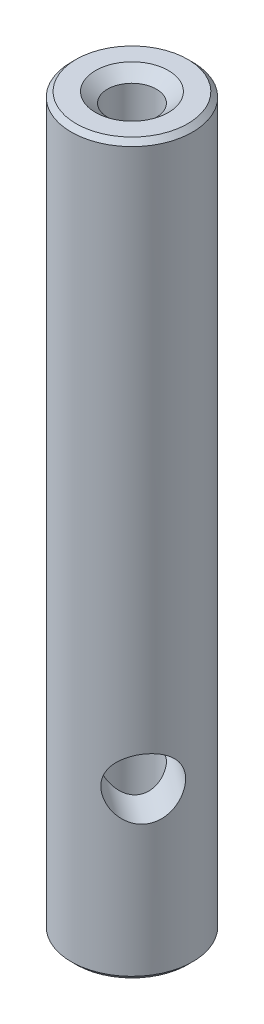
SolidWorks part; units mm, degrees
ref_plane "Front Plane" through (0, 0, 0) normal (0, 0, 1) x (1, 0, 0)
ref_plane "Top Plane" through (0, 0, 0) normal (0, 1, 0) x (1, 0, 0)
ref_plane "Right Plane" through (0, 0, 0) normal (1, 0, 0) x (0, 0, -1)
ref_plane "Plane1" through (0, 0, 0) normal (0, 0, -1) x (-1, 0, 0)
sketch "Sketch1" plane through (0, 0, 0) normal (0, 0, -1) x (-1, 0, 0)
  line L0 (-5.8382, 0) -> (0, 0)
  line L1 (0, 0) -> (0, 76.2)
  line L2 (0, 76.2) -> (-5.8382, 76.2)
  line L3 (-5.8382, 76.2) -> (-6.3462, 75.692)
  line L4 (-6.3462, 75.692) -> (-6.3462, 0.508)
  line L5 (-6.3462, 0.508) -> (-5.8382, 0)
  line L6 (0, 0) -> (0, 76.2) construction
revolve "Revolve1" add sketch "Sketch1" angle 360 about L6
hole_wizard "1/4-20 Tapped Hole1" positions "Sketch2" profile "Sketch3" tap size "1/4-20" standard "ANSI Inch" end condition up to next
sketch "Sketch2" plane through (0, 76.2, 0) normal (0, 1, 0) x (1, 0, 0)
  point P0 (0, 0)
sketch "Sketch3" plane through (0, 76.2, 0) normal (1, 0, 0) x (0, 0, 1)
  line L0 (0, 0) -> (0, 76.2)
  line L1 (0, 76.2) -> (2.5527, 76.2)
  line L2 (2.5527, 76.2) -> (2.5527, 1.055)
  line L3 (2.5527, 1.055) -> (3.81, 0)
  line L5 (3.81, 0) -> (0, 0)
  line L6 (-2.5527, 1.055) -> (-3.81, 0) construction
  line L11 (0, -6.35) -> (0, 107.95) construction
  dimension "Thru Tap Drill Dia." = 5.1054
  dimension "Thru Tap Drill Depth" = 76.2
  dimension "Near C'Sink Dia." = 7.62
  dimension "Near C'Sink Angle" = 100
cosmetic thread "Hole Thread1"
hole_wizard "1/4 (0.25) Diameter Hole1" positions "3DSketch1" profile "Sketch4" hole size "1/4" standard "ANSI Inch" end condition through all
sketch3d "3DSketch1"
  point P0 (-5.1147, 17.4308, -3.7569)
sketch "Sketch4" plane through (-5.1147, 17.4308, -3.7569) normal (0, 1, 0) x (-0.592, 0, 0.8059)
  line L0 (0, 0) -> (0, 15.2178)
  line L1 (0, 15.2178) -> (3.175, 15.2178)
  line L2 (3.175, 15.2178) -> (3.175, 0)
  line L5 (3.175, 0) -> (0, 0)
  line L11 (0, -6.35) -> (0, 107.95) construction
  dimension "Thru Hole Dia." = 6.35
  dimension "Thru Hole Depth" = 15.2178
